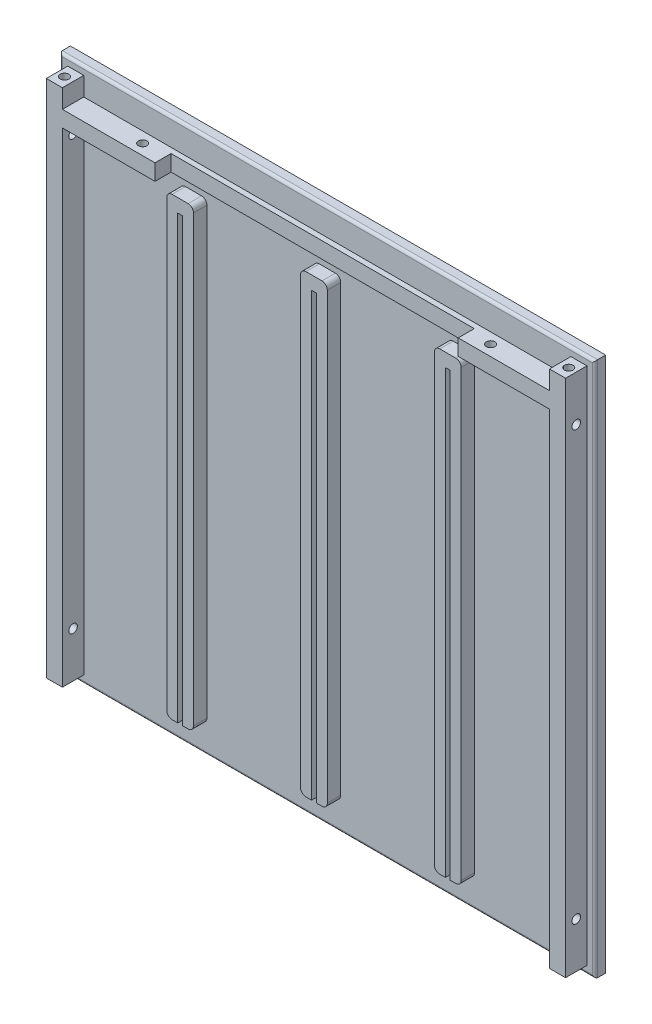
SolidWorks part; units mm, degrees
ref_plane "Plan de face" through (0, 0, 0) normal (0, 0, 1) x (1, 0, 0)
ref_plane "Plan de dessus" through (0, 0, 0) normal (0, 1, 0) x (1, 0, 0)
ref_plane "Plan de droite" through (0, 0, 0) normal (1, 0, 0) x (0, 0, -1)
sketch "Esquisse1" plane through (0, 0, 0) normal (0, 0, 1) x (1, 0, 0)
  line L1 (0, 0) -> (200, 0)
  line L2 (0, 0) -> (0, 200)
  line L3 (0, 200) -> (200, 200)
  line L4 (200, 0) -> (200, 200)
  dimension "D1" = 200
  dimension "D2" = 200
extrude "Boss.-Extru. Paroie" add sketch "Esquisse1" along normal blind 4
sketch "Esquisse2" plane through (0, 0, 4) normal (0, 0, 1) x (1, 0, 0)
  line L0 (0, 0) -> (200, 0) construction
  line L1 (47, 180) -> (53, 180)
  line L2 (45, 178) -> (45, 12)
  line L3 (47, 10) -> (53, 10)
  line L4 (55, 178) -> (55, 12)
  line L5 (0, 200) -> (0, 0) construction
  line L18 (97, 180) -> (103, 180)
  line L19 (95, 178) -> (95, 12)
  line L20 (97, 10) -> (103, 10)
  line L21 (105, 178) -> (105, 12)
  line L22 (147, 180) -> (153, 180)
  line L23 (145, 178) -> (145, 12)
  line L24 (147, 10) -> (153, 10)
  line L25 (155, 178) -> (155, 12)
  arc A0 (45, 12) -> (47, 10) centre (47, 12) ccw
  arc A1 (53, 10) -> (55, 12) centre (53, 12) ccw
  arc A2 (53, 180) -> (55, 178) centre (53, 178) cw
  arc A3 (47, 180) -> (45, 178) centre (47, 178) ccw
  arc A16 (95, 12) -> (97, 10) centre (97, 12) ccw
  arc A17 (103, 10) -> (105, 12) centre (103, 12) ccw
  arc A18 (103, 180) -> (105, 178) centre (103, 178) cw
  arc A19 (97, 180) -> (95, 178) centre (97, 178) ccw
  arc A20 (145, 12) -> (147, 10) centre (147, 12) ccw
  arc A21 (153, 10) -> (155, 12) centre (153, 12) ccw
  arc A22 (153, 180) -> (155, 178) centre (153, 178) cw
  arc A23 (147, 180) -> (145, 178) centre (147, 178) ccw
  point P10 (45, 10)
  point P15 (55, 180)
  point P18 (45, 180)
  dimension "D5" = 2
  dimension "D1" = 10
  dimension "D2" = 170
  dimension "D3" = 10
  dimension "D4" = 45
  dimension "D6" = 3
sketch "Esquisse4" plane through (0, 0, 4) normal (0, 0, 1) x (1, 0, 0)
  line L0 (3, 3) -> (9, 3)
  line L6 (0, 0) -> (200, 0) construction
  line L17 (9, 3) -> (9, 184)
  line L18 (9, 184) -> (191, 184)
  line L19 (191, 184) -> (191, 3)
  line L20 (191, 3) -> (197, 3)
  line L21 (197, 3) -> (197, 197)
  line L22 (197, 197) -> (191, 197)
  line L24 (191, 197) -> (191, 190)
  line L26 (191, 190) -> (9, 190)
  line L27 (9, 190) -> (9, 197)
  line L28 (9, 197) -> (3, 197)
  line L29 (3, 197) -> (3, 3)
  line L31 (0, 200) -> (0, 0) construction
  line L32 (200, 200) -> (0, 200) construction
  line L33 (200, 0) -> (200, 200) construction
  dimension "D1" = 6
  dimension "D2" = 3
  dimension "D3" = 3
  dimension "D4" = 6
  dimension "D5" = 6
  dimension "D6" = 3
  dimension "D7" = 3
  dimension "D8" = 6
  dimension "D9" = 3
  dimension "D10" = 10
  dimension "D11" = 3
  dimension "D12" = 6
extrude "Boss.-Extru. Bords" add sketch "Esquisse4" along normal blind 8
extrude "Boss.-Extru. Glissieres" add sketch "Esquisse2" along normal blind 5
fillet "Congé1" radius 1 4 edges at (200, 100, 4) (100, 200, 4) (0, 100, 4) (100, 0, 4)
sketch "Esquisse8" plane through (0, 0, 4) normal (0, 0, 1) x (1, 0, 0)
  line L0 (0, 200) -> (0, 0) construction
  line L1 (99.1, 175) -> (100.9, 175)
  line L2 (99.1, 175) -> (99.1, -5)
  line L3 (99.1, -5) -> (100.9, -5)
  line L4 (100.9, 175) -> (100.9, -5)
  line L5 (200, 200) -> (0, 200) construction
  line L6 (149.1, 175) -> (150.9, 175)
  line L7 (149.1, 175) -> (149.1, -5)
  line L8 (149.1, -5) -> (150.9, -5)
  line L9 (150.9, 175) -> (150.9, -5)
  line L10 (49.1, 175) -> (50.9, 175)
  line L11 (49.1, 175) -> (49.1, -5)
  line L12 (49.1, -5) -> (50.9, -5)
  line L13 (50.9, 175) -> (50.9, -5)
  dimension "D1" = 1.8
  dimension "D2" = 99.1
  dimension "D3" = 180
  dimension "D4" = 25
  dimension "D5" = 2
  dimension "D6" = 2
extrude "Enlèv. mat.-Extru.6" cut sketch "Esquisse8" along normal through all
sketch "Esquisse5" plane through (3, 0, 0) normal (-1, 0, 0) x (0, 0, 1)
  line L0 (12, 3) -> (4, 3) construction
  line L1 (12, 197) -> (4, 197) construction
  circle A0 centre (8, 180) radius 1.6
  circle A1 centre (8, 20) radius 1.6
  dimension "D1" = 17
  dimension "D2" = 17
extrude "Enlèv. mat.-Extru.2" cut sketch "Esquisse5" against normal blind 10
sketch "Esquisse6" plane through (197, 0, 0) normal (1, 0, 0) x (0, 0, -1)
  line L0 (0, 0) -> (0, 200) construction
  line L1 (-12, 197) -> (-4, 197) construction
  line L2 (-12, 3) -> (-4, 3) construction
  circle A0 centre (-8, 180) radius 1.6
  circle A1 centre (-8, 20) radius 1.6
  dimension "D1" = 8
  dimension "D2" = 3.2
  dimension "D3" = 17
  dimension "D4" = 17
extrude "Enlèv. mat.-Extru.3" cut sketch "Esquisse6" against normal blind 10
sketch "Esquisse7" plane through (0, 184, 0) normal (0, -1, 0) x (1, 0, 0)
  line L0 (9, 12) -> (191, 12) construction
  line L1 (9, 12) -> (9, 4) construction
  line L2 (50, 4) -> (50, 17.1304) construction
  line L3 (9, 4) -> (191, 4) construction
  circle A0 centre (35, 8) radius 1.6
  circle A1 centre (165, 8) radius 1.6
  dimension "D1" = 4
  dimension "D4" = 15
  dimension "D5" = 26
  dimension "D2" = 4
  dimension "D3" = 130
extrude "Enlèv. mat.-Extru.4" cut sketch "Esquisse7" against normal blind 10
sketch "Esquisse9" plane through (0, 197, 0) normal (0, 1, 0) x (1, 0, 0)
  line L0 (200, -3) -> (200, 0) construction
  line L2 (0, -3) -> (0, 0) construction
  line L4 (200, 0) -> (0, 0) construction
  circle A0 centre (194.2, -8) radius 1.6
  circle A1 centre (5.8, -8) radius 1.6
  dimension "D1" = 5.8
  dimension "D3" = 5.8
  dimension "D2" = 8
  dimension "D4" = 8
sketch "Esquisse10" plane through (0, 3, 0) normal (0, -1, 0) x (-1, 0, 0)
  circle A0 centre (-194.2, -8) radius 1.6
  circle A1 centre (-5.8, -8) radius 1.6
extrude "Enlèv. mat.-Extru.8" cut sketch "Esquisse10" against normal blind 10
sketch "Esquisse11" plane through (0, 0, 12) normal (0, 0, 1) x (1, 0, 0)
  line L0 (191, 190) -> (9, 190) construction
  line L1 (156.9004, 190) -> (43.5972, 190)
  line L2 (156.9004, 190) -> (156.9004, 184)
  line L3 (156.9004, 184) -> (43.5972, 184)
  line L4 (43.5972, 190) -> (43.5972, 184)
  line L5 (9, 184) -> (191, 184) construction
extrude "Enlèv. mat.-Extru.9" cut sketch "Esquisse11" against normal blind 6
extrude "Enlèv. mat.-Extru.10" cut sketch "Esquisse9" against normal blind 10
